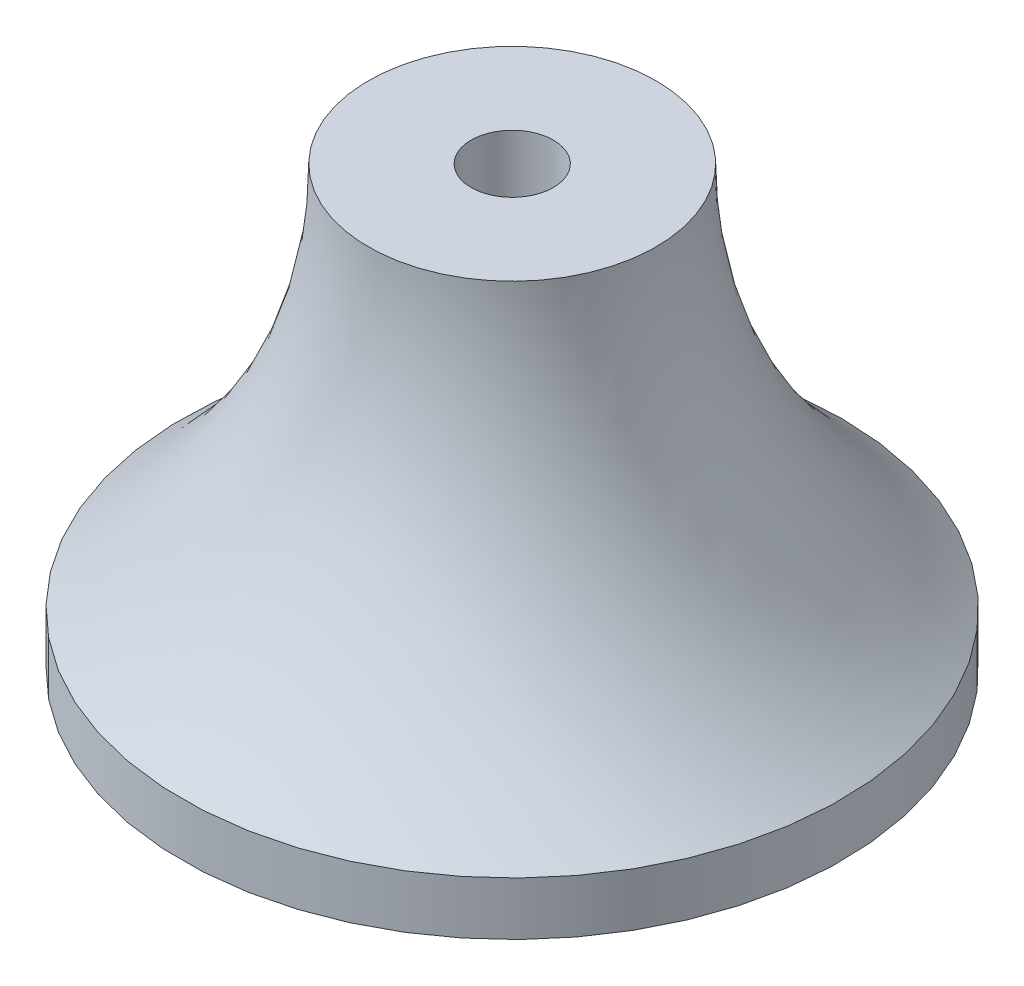
SolidWorks part; units mm, degrees
ref_plane "Front Plane" through (0, 0, 0) normal (0, 0, 1) x (1, 0, 0)
ref_plane "Top Plane" through (0, 0, 0) normal (0, 1, 0) x (1, 0, 0)
ref_plane "Right Plane" through (0, 0, 0) normal (1, 0, 0) x (0, 0, -1)
sketch "Sketch2" plane through (0, 0, 0) normal (0, 0, 1) x (1, 0, 0)
  line L0 (0, 0) -> (0, 19.05) construction
  line L2 (2.032, -2.6342) -> (2.032, 19.05)
  line L3 (7.112, 19.05) -> (7.112, -2.6342)
  line L5 (2.032, 19.05) -> (7.112, 19.05)
  line L6 (2.032, 0) -> (16.2956, 0)
  line L8 (2.032, -2.6342) -> (16.2956, -2.6342)
  line L9 (16.2956, 0) -> (16.2956, -2.6342)
  arc A0 (7.112, 19.05) -> (16.2956, 0) centre (31.4619, 19.05) ccw
  dimension "D1" = 2.032
  dimension "D2" = 16.2956
  dimension "D3" = 19.05
  dimension "D5" = 2.6342
  dimension "D6" = 5.08
revolve "Revolve1" add sketch "Sketch2" angle 360 about L0
sketch "Sketch3" plane through (0, -2.6342, 0) normal (0, -1, 0) x (1, 0, 0)
  line L1 (4.8078, 0.5521) -> (1.9257, 4.4397)
  line L2 (1.9257, 4.4397) -> (-2.882, 3.8876)
  line L3 (-2.882, 3.8876) -> (-4.8078, -0.5521)
  line L4 (-4.8078, -0.5521) -> (-1.9257, -4.4397)
  line L5 (-1.9257, -4.4397) -> (2.882, -3.8876)
  line L6 (2.882, -3.8876) -> (4.8078, 0.5521)
  circle A0 centre (0, 0) radius 4.191 construction
  dimension "D1" = 8.382
  dimension "D2" = 9.6155
extrude "Cut-Extrude1" cut sketch "Sketch3" against normal offset from surface (16.0962 mm away) 5.588 up to face at (0, 19.05, -7.112)
